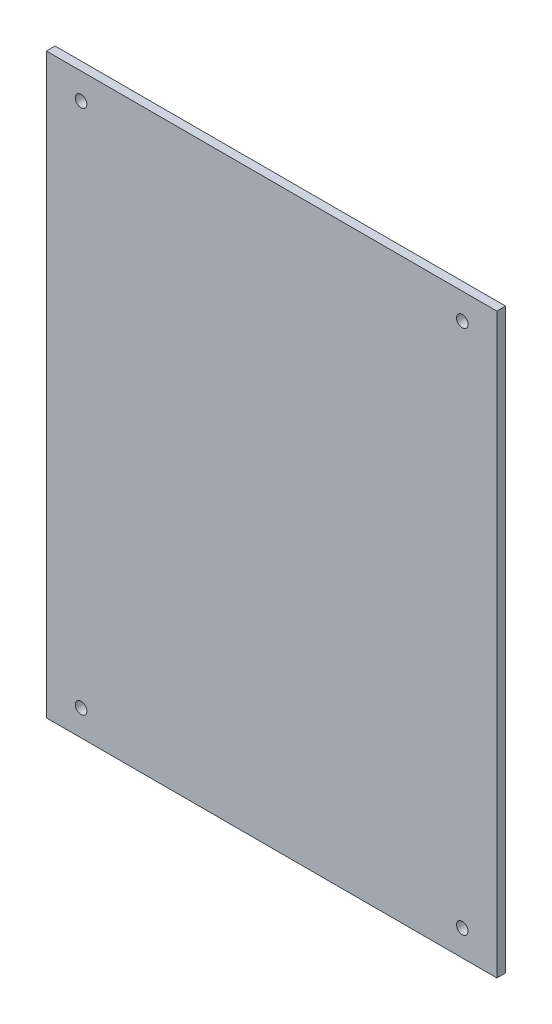
SolidWorks part; units mm, degrees
ref_plane "Plan de face" through (0, 0, 0) normal (0, 0, 1) x (1, 0, 0)
ref_plane "Plan de dessus" through (0, 0, 0) normal (0, 1, 0) x (1, 0, 0)
ref_plane "Plan de droite" through (0, 0, 0) normal (1, 0, 0) x (0, 0, -1)
sketch "Esquisse1" plane through (0, 0, 0) normal (0, 0, 1) x (1, 0, 0)
  line L1 (0, 0) -> (156, 0)
  line L2 (0, 0) -> (0, 200)
  line L3 (0, 200) -> (156, 200)
  line L4 (156, 0) -> (156, 200)
  dimension "D1" = 200
  dimension "D2" = 156
extrude "Boss.-Extru.1" add sketch "Esquisse1" along normal blind 3
sketch "Esquisse2" plane through (0, 0, 3) normal (0, 0, 1) x (1, 0, 0)
  line L0 (0, 100) -> (156, 100) construction
  line L1 (0, 200) -> (0, 0) construction
  line L2 (156, 0) -> (156, 200) construction
  line L3 (78, 200) -> (78, 0) construction
  line L4 (156, 200) -> (0, 200) construction
  line L5 (0, 0) -> (156, 0) construction
  circle A0 centre (12, 9) radius 2
  circle A1 centre (144, 9) radius 2
  circle A2 centre (144, 191) radius 2
  circle A3 centre (12, 191) radius 2
  dimension "D1" = 9
  dimension "D2" = 12
  dimension "D3" = 4
extrude "Enlèv. mat.-Extru.1" cut sketch "Esquisse2" against normal blind 3
